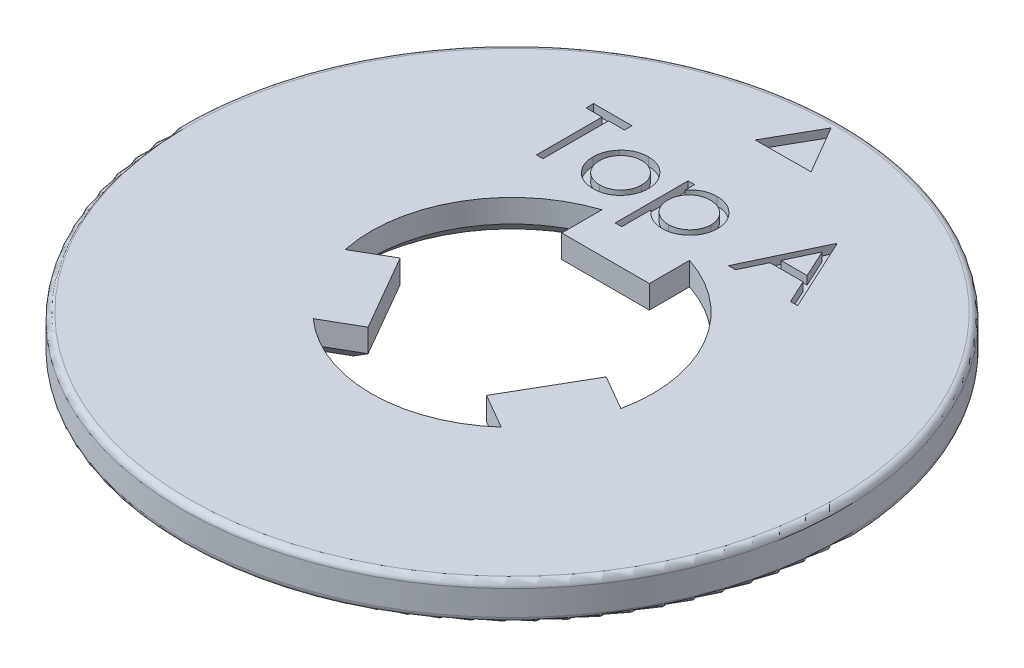
SolidWorks part; units mm, degrees
ref_plane "Front Plane" through (0, 0, 0) normal (0, 0, 1) x (1, 0, 0)
ref_plane "Top Plane" through (0, 0, 0) normal (0, 1, 0) x (1, 0, 0)
ref_plane "Right Plane" through (0, 0, 0) normal (1, 0, 0) x (0, 0, -1)
sketch "Sketch1" plane through (0, 0, 0) normal (0, 1, 0) x (1, 0, 0)
  line L0 (0, -15.8) -> (0, 15.8) construction
  line L1 (-15.8, 0) -> (15.8, 0) construction
  line L60 (6.6062, -1.3857) -> (4.9381, -0.4226)
  line L62 (-2.1031, 6.414) -> (-2.1031, 4.4878)
  line L63 (-2.1031, 4.4878) -> (2.0969, 4.4878)
  line L64 (2.0969, 6.416) -> (2.0969, 4.4878)
  line L68 (4.508, -5.024) -> (2.8381, -4.0599)
  line L69 (4.9381, -0.4226) -> (2.8381, -4.0599)
  line L70 (-4.5031, -5.0283) -> (-2.835, -4.0652)
  line L72 (-6.6049, -1.3921) -> (-4.935, -0.4279)
  line L73 (-2.835, -4.0652) -> (-4.935, -0.4279)
  circle A0 centre (0, 0) radius 15.8
  arc A5 (-2.1031, 6.414) -> (-6.6049, -1.3921) centre (0, 0) ccw
  arc A6 (-4.5031, -5.0283) -> (4.508, -5.024) centre (0, 0) ccw
  arc A7 (6.6062, -1.3857) -> (2.0969, 6.416) centre (0, 0) ccw
  point P3 (0, 9.9)
  point P11 (0, 6.1614)
  point P26 (0, 0)
  point P40 (0, 0)
  point P42 (0, 0)
  point P43 (0, 0)
  point P44 (0, 0)
  dimension "D6" = 3
  dimension "D5" = 4.2
extrude "Boss-Extrude1" add sketch "Sketch1" along normal blind 1.8
fillet "Fillet1" radius 0.3 2 edges at (0, 0, 15.8) (0, 1.8, 15.8)
ref_plane "Plane1" through (0, 1.8, 0) normal (0, 1, 0) x (1, 0, 0)
sketch "Sketch3" plane through (0, 1.8, 0) normal (0, 1, 0) x (1, 0, 0)
  line L0 (0, 0) -> (0, 13.6609) construction
  line L2 (-1.3308, 12.9858) -> (1.34, 13.0017)
  line L3 (1.34, 13.0017) -> (-0.0092, 15.3068)
  line L4 (-0.0092, 15.3068) -> (-1.3308, 12.9858)
  circle A0 centre (0, 13.7648) radius 0.771 construction
extrude "Cut-Extrude1" cut sketch "Sketch3" against normal blind 0.4
sketch "Sketch4" plane through (0, 1.8, 0) normal (0, 1, 0) x (1, 0, 0)
  line L0 (-8.3279, 7.1231) -> (8.3197, 7.1231) construction
  text T0 "Top A"
extrude "Cut-Extrude2" cut sketch "Sketch4" against normal blind 0.4
scale "Scale1" scale about centroid uniform scaling yes scale factor 1.15
chamfer "Chamfer1" distance 0.8 angle 45 12 edges at (6.6378, -0.1346, 1.0334) (4.4711, -0.1346, 2.5711) (4.2238, -0.1346, 5.2169) (0.0035, -0.1346, 7.7562) (-4.2196, -0.1346, 5.2225) (-4.468, -0.1346, 2.5773) (-6.6357, -0.1346, 1.0402) (-6.7246, -0.1346, -3.8843) (-2.4188, -0.1346, -6.2749) (-0.0038, -0.1346, -5.1673) (2.4112, -0.1346, -6.276) (6.7204, -0.1346, -3.8908)
